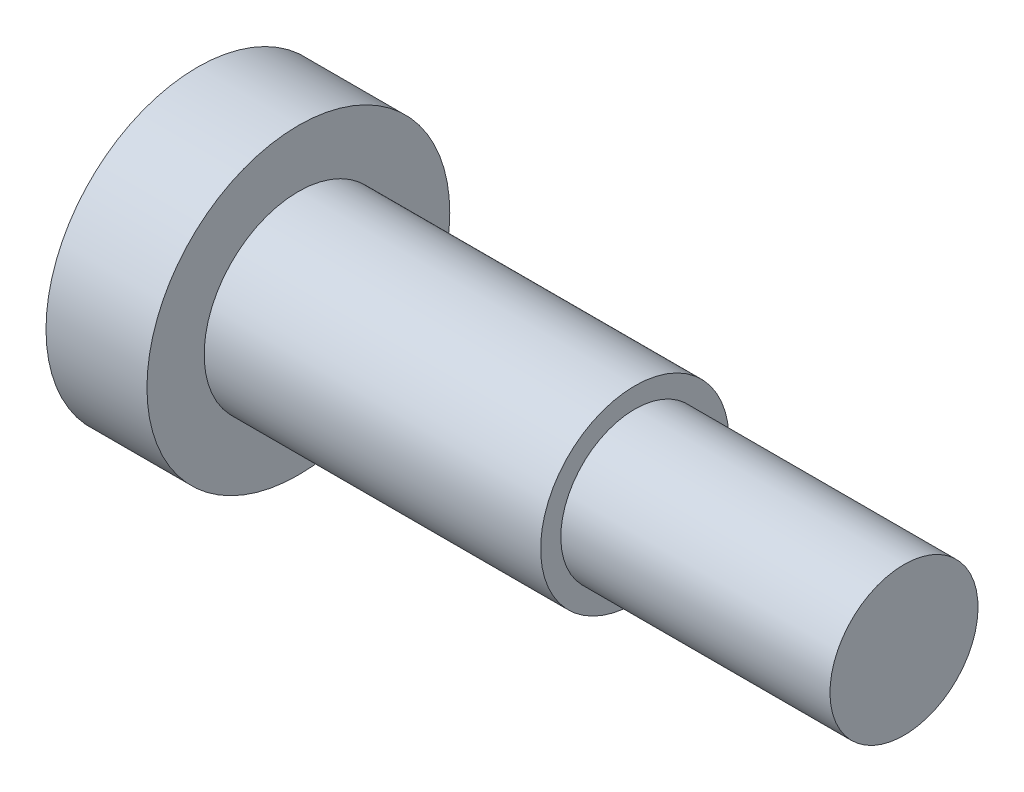
SolidWorks part; units mm, degrees
ref_plane "Front Plane" through (0, 0, 0) normal (0, 0, 1) x (1, 0, 0)
ref_plane "Top Plane" through (0, 0, 0) normal (0, 1, 0) x (1, 0, 0)
ref_plane "Right Plane" through (0, 0, 0) normal (1, 0, 0) x (0, 0, -1)
sketch "Sketch7" plane through (0, 0, 0) normal (0, 0, 1) x (1, 0, 0)
  line L0 (0, 0) -> (0, 22.5)
  line L1 (0, 22.5) -> (15, 22.5)
  line L2 (15, 22.5) -> (15, 14)
  line L3 (15, 14) -> (65, 14)
  line L4 (65, 14) -> (65, 11)
  line L5 (65, 11) -> (105, 11)
  line L6 (105, 11) -> (105, 0)
  line L7 (105, 0) -> (0, 0)
  dimension "D1" = 15
  dimension "D2" = 50
  dimension "D3" = 105
  dimension "D4" = 3
  dimension "D5" = 22.5
  dimension "D6" = 11
revolve "Revolve1" add sketch "Sketch7" angle 360 about L7
